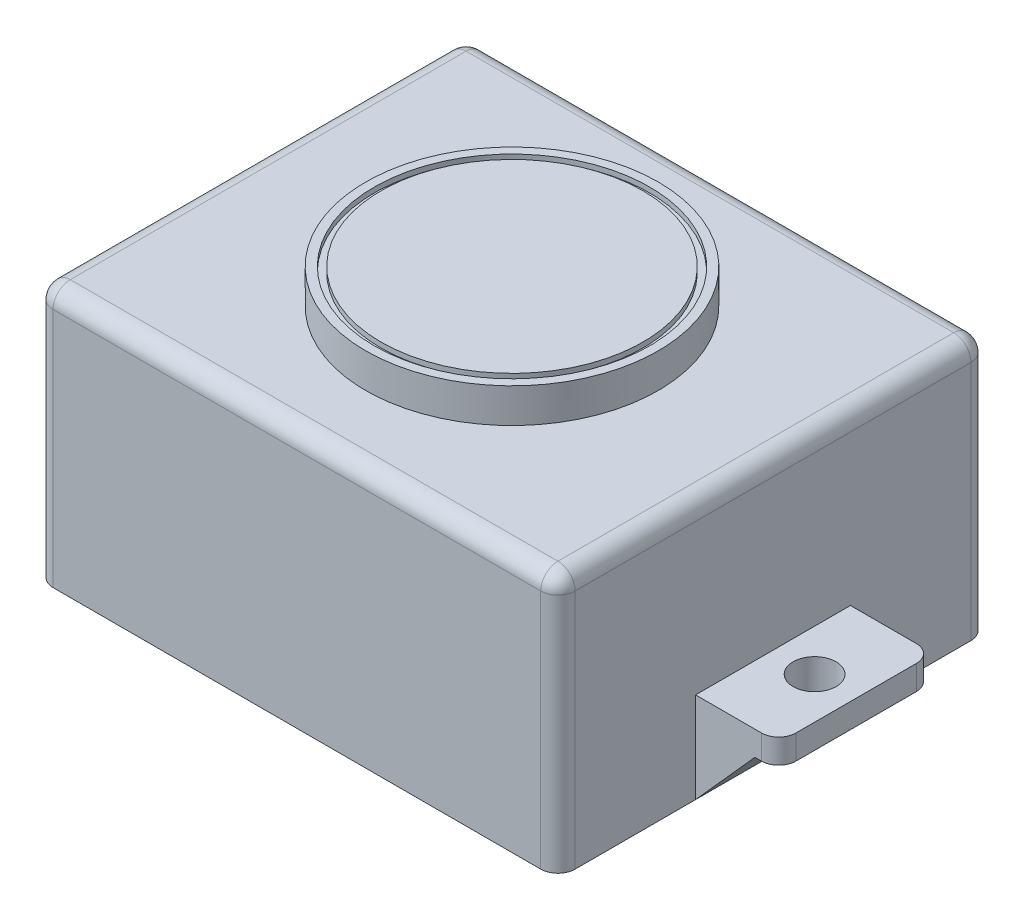
SolidWorks part; units mm, degrees
ref_plane "Front Plane" through (0, 0, 0) normal (0, 0, 1) x (1, 0, 0)
ref_plane "Top Plane" through (0, 0, 0) normal (0, 1, 0) x (1, 0, 0)
ref_plane "Right Plane" through (0, 0, 0) normal (1, 0, 0) x (0, 0, -1)
sketch "Sketch1" plane through (0, 0, 0) normal (0, 0, 1) x (1, 0, 0)
  line L1 (-503.924, 236.8378) -> (266.6571, 236.8378)
  line L2 (-626.6334, -10.2973) -> (-626.6334, -46.3378)
  line L3 (-503.924, -144.1622) -> (266.6571, -144.1622)
  line L4 (389.3666, -10.2973) -> (389.3666, -46.3378)
  line L6 (-626.6334, -10.2973) -> (-503.924, -10.2973)
  line L7 (-503.924, -10.2973) -> (-503.924, 236.8378)
  line L10 (389.3666, -10.2973) -> (266.6571, -10.2973)
  line L11 (266.6571, -10.2973) -> (266.6571, 236.8378)
  line L12 (389.3666, -46.3378) -> (354.1841, -46.3378)
  line L13 (354.1841, -46.3378) -> (266.6571, -144.1622)
  line L14 (-626.6334, -46.3378) -> (-591.451, -46.3378)
  line L15 (-591.451, -46.3378) -> (-503.924, -144.1622)
  dimension "D1" = 381
  dimension "D2" = 1016
  dimension "D3" = 770.5811
extrude "Boss-Extrude1" add sketch "Sketch1" along normal blind 635
sketch "Sketch2" plane through (0, 236.8378, 0) normal (0, 1, 0) x (1, 0, 0)
  line L0 (-626.6334, -635) -> (-626.6334, 0) construction
  line L1 (-626.6334, -203.2) -> (-503.924, -203.2)
  line L2 (-626.6334, -203.2) -> (-626.6334, 0)
  line L3 (-626.6334, 0) -> (-503.924, 0)
  line L4 (-503.924, -203.2) -> (-503.924, 0)
  line L5 (266.6571, 0) -> (-503.924, 0) construction
  line L6 (-503.924, -635) -> (-503.924, 0) construction
  line L11 (-503.924, -635) -> (-626.6334, -635) construction
  line L12 (-626.6334, -635) -> (-503.924, -635)
  line L13 (-626.6334, -635) -> (-626.6334, -431.8)
  line L14 (-626.6334, -431.8) -> (-503.924, -431.8)
  line L15 (-503.924, -635) -> (-503.924, -431.8)
  line L16 (-503.924, -635) -> (-503.924, 0) construction
  line L17 (266.6571, -635) -> (266.6571, 0) construction
  line L18 (389.3666, -635) -> (266.6571, -635)
  line L19 (389.3666, -635) -> (389.3666, -431.8)
  line L20 (389.3666, -431.8) -> (266.6571, -431.8)
  line L21 (266.6571, -635) -> (266.6571, -431.8)
  line L22 (266.6571, -635) -> (266.6571, 0) construction
  line L23 (389.3666, 0) -> (266.6571, 0)
  line L24 (389.3666, 0) -> (389.3666, -203.2)
  line L25 (389.3666, -203.2) -> (266.6571, -203.2)
  line L26 (266.6571, 0) -> (266.6571, -203.2)
  dimension "D1" = 203.2
extrude "Cut-Extrude1" cut sketch "Sketch2" against normal through all
sketch "Sketch3" plane through (0, -10.2973, 0) normal (0, 1, 0) x (1, 0, 0)
  circle A0 centre (-565.2787, -317.5) radius 31.75
  circle A1 centre (328.0118, -317.5) radius 31.75
  dimension "D1" = 63.5
extrude "Cut-Extrude2" cut sketch "Sketch3" against normal blind 88.9
fillet "Fillet1" radius 25.4 4 edges at (389.3666, -28.3176, 203.2) (389.3666, -28.3176, 431.8) (-626.6334, -28.3176, 203.2) (-626.6334, -28.3176, 431.8)
fillet "Fillet2" radius 25.4 8 edges at (266.6571, 46.3378, 0) (266.6571, 46.3378, 635) (266.6571, 236.8378, 317.5) (-118.6334, 236.8378, 0) (-503.924, 236.8378, 317.5) (-503.924, 46.3378, 0) (-503.924, 46.3378, 635) (-118.6334, 236.8378, 635)
sketch "Sketch4" plane through (0, 236.8378, 0) normal (0, 1, 0) x (1, 0, 0)
  circle A0 centre (-118.6334, -317.5) radius 215.9
  dimension "D1" = 431.8
extrude "Boss-Extrude2" add sketch "Sketch4" along normal blind 50.8
sketch "Sketch5" plane through (0, 287.6378, 0) normal (0, 1, 0) x (1, 0, 0)
  circle A0 centre (-118.6334, -317.5) radius 203.2
  dimension "D1" = 406.4
extrude "Cut-Extrude3" cut sketch "Sketch5" against normal blind 7.62
sketch "Sketch6" plane through (0, 280.0178, 0) normal (0, 1, 0) x (1, 0, 0)
  circle A0 centre (-118.6334, -317.5) radius 193.3975
extrude "Boss-Extrude3" add sketch "Sketch6" along normal blind 7.62 separate body
scale "Scale1" bodies to scale 106 105 scale about origin uniform scaling yes scale factor 0.01
